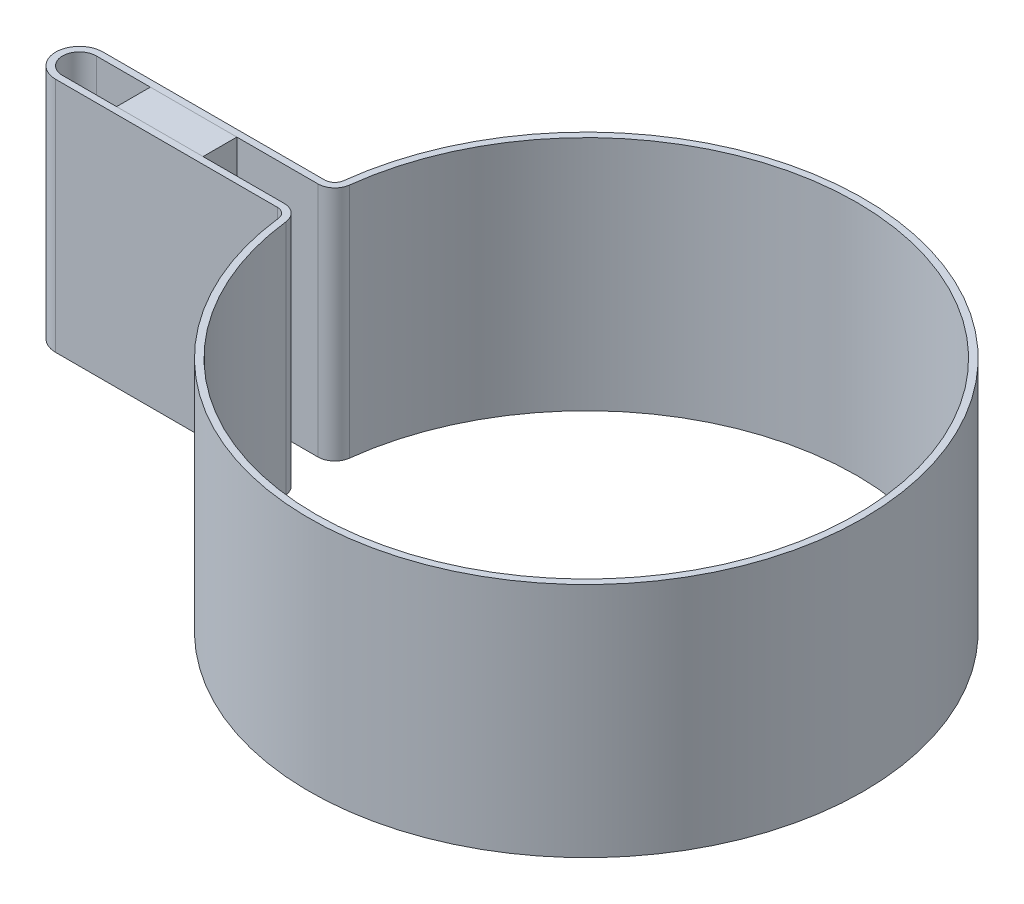
SolidWorks part; units mm, degrees
other "COLL.BOX-Boss-Extrude2"
ref_plane "Front Plane" through (0, 0, 0) normal (0, 0, 1) x (1, 0, 0)
ref_plane "Top Plane" through (0, 0, 0) normal (0, 1, 0) x (1, 0, 0)
ref_plane "Right Plane" through (0, 0, 0) normal (1, 0, 0) x (0, 0, -1)
sketch "Sketch1" plane through (0, 0, 0) normal (0, 1, 0) x (1, 0, 0)
  line L0 (-75, 3.5) -> (-42.2049, 3.5)
  line L1 (-75, 2.5) -> (-42.2049, 2.5)
  line L3 (-75, -2.5) -> (-42.2049, -2.5)
  line L5 (-75, -3.5) -> (-42.2049, -3.5)
  arc A0 (-39.7222, -4.7059) -> (-39.7222, 4.7059) centre (0, 0) ccw
  arc A1 (-75, 2.5) -> (-75, -2.5) centre (-75, 0) ccw
  arc A2 (-42.2049, 2.5) -> (-39.7222, 4.7059) centre (-42.2049, 5) ccw
  arc A3 (-39.7222, -4.7059) -> (-42.2049, -2.5) centre (-42.2049, -5) ccw
  arc A4 (-42.2049, 3.5) -> (-40.7153, 4.8235) centre (-42.2049, 5) ccw
  arc A5 (-40.7153, -4.8235) -> (-40.7153, 4.8235) centre (0, 0) ccw
  arc A6 (-40.7153, -4.8235) -> (-42.2049, -3.5) centre (-42.2049, -5) ccw
  arc A7 (-75, 3.5) -> (-75, -3.5) centre (-75, 0) ccw
  point P3 (-57.4609, 0)
  dimension "D1" = 80
  dimension "D3" = 5
  dimension "D5" = 5
  dimension "D6" = 5
  dimension "D2" = 5
  dimension "D4" = 75
  dimension "D7" = 1
extrude "Boss-Extrude1" add sketch "Sketch1" along normal blind 35
sketch "Sketch2" plane through (0, 35, 0) normal (0, 1, 0) x (1, 0, 0)
  line L0 (-42.2049, 3.5) -> (-75, 3.5) construction
  line L1 (-67, 3.5) -> (-54.2049, 3.5)
  line L2 (-67, 3.5) -> (-67, -3.5)
  line L3 (-67, -3.5) -> (-54.2049, -3.5)
  line L4 (-54.2049, 3.5) -> (-54.2049, -3.5)
  line L5 (-75, -3.5) -> (-42.2049, -3.5) construction
  arc A0 (-75, 3.5) -> (-75, -3.5) centre (-75, 0) ccw construction
  dimension "D1" = 8
  dimension "D2" = 12
extrude "Boss-Extrude2" add sketch "Sketch2" against normal up to vertex (35 mm away) separate body
